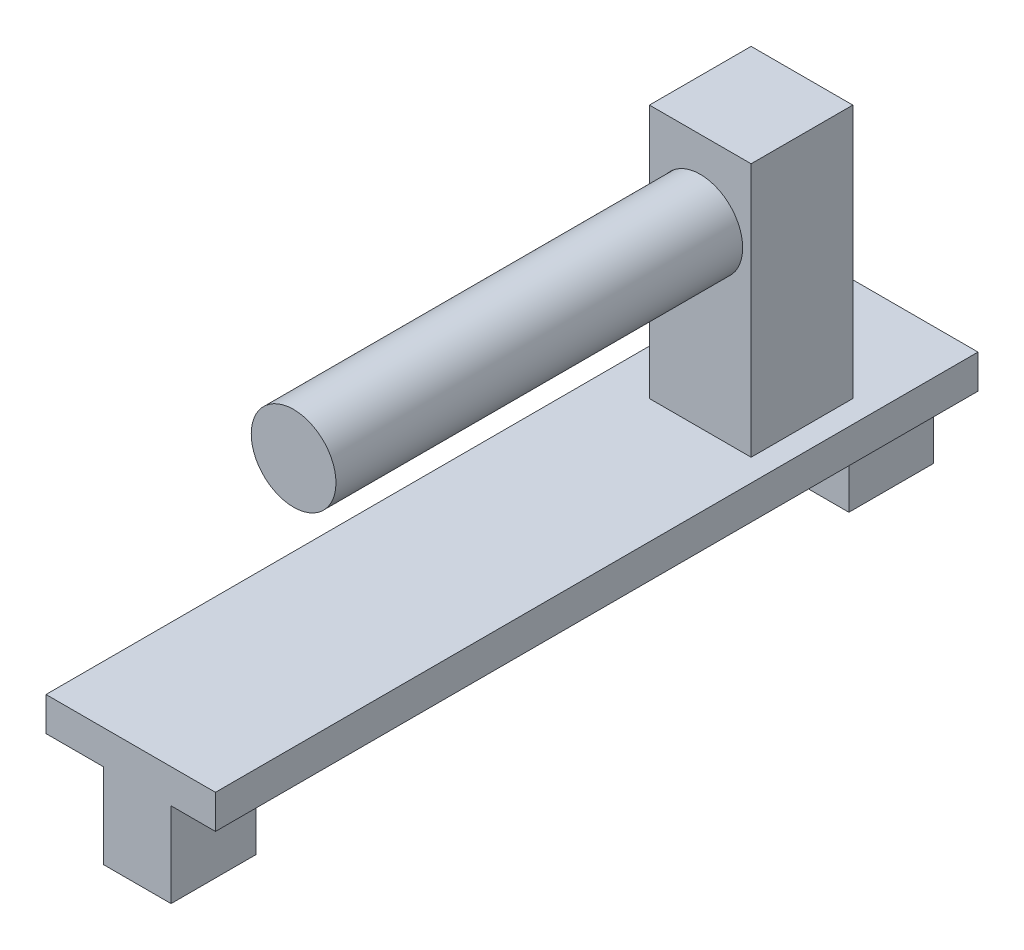
SolidWorks part; units mm, degrees
ref_plane "Front Plane" through (0, 0, 0) normal (0, 0, 1) x (1, 0, 0)
ref_plane "Top Plane" through (0, 0, 0) normal (0, 1, 0) x (1, 0, 0)
ref_plane "Right Plane" through (0, 0, 0) normal (1, 0, 0) x (0, 0, -1)
sketch "Sketch1" plane through (0, 0, 0) normal (0, 1, 0) x (1, 0, 0)
  line L1 (-3, -3) -> (3, -3)
  line L2 (-3, -3) -> (-3, 3)
  line L3 (-3, 3) -> (3, 3)
  line L4 (3, -3) -> (3, 3)
  line L5 (-3, -3) -> (3, 3) construction
  line L6 (-3, 3) -> (3, -3) construction
  point P0 (0, 0)
  dimension "D1" = 6
  dimension "D2" = 6
extrude "Boss-Extrude1" add sketch "Sketch1" along normal blind 15
sketch "Sketch3" plane through (0, 0, 0) normal (0, 1, 0) x (1, 0, 0)
  line L0 (4.3176, 9.0713) -> (-5.6824, 9.0713)
  line L1 (4.3176, 9.0713) -> (4.3176, -35.9287)
  line L2 (-5.6824, 9.0713) -> (-5.6824, -35.9287)
  line L3 (4.3176, -35.9287) -> (-5.6824, -35.9287)
  dimension "D1" = 45
  dimension "D2" = 10
extrude "Boss-Extrude2" add sketch "Sketch3" against normal blind 2
sketch "Sketch4" plane through (0, 0, 35.9287) normal (0, 0, 1) x (1, 0, 0)
  line L0 (-2.3022, -2) -> (1.6978, -2)
  line L1 (-2.3022, -2) -> (-2.3022, -7)
  line L2 (1.6978, -2) -> (1.6978, -7)
  line L3 (-2.3022, -7) -> (1.6978, -7)
  line L4 (-5.6824, -2) -> (4.3176, -2) construction
  dimension "D1" = 5
  dimension "D2" = 4
extrude "Boss-Extrude3" add sketch "Sketch4" against normal blind 2
sketch "Sketch5" plane through (0, 0, -9.0713) normal (0, 0, -1) x (-1, 0, 0)
  line L0 (-1.6978, -2) -> (2.3022, -2)
  line L1 (-1.6978, -2) -> (-1.6978, -7)
  line L2 (2.3022, -2) -> (2.3022, -7)
  line L3 (-1.6978, -7) -> (2.3022, -7)
  dimension "D1" = 4
  dimension "D2" = 5
extrude "Boss-Extrude4" add sketch "Sketch5" against normal blind 2
sketch "Sketch6" plane through (0, 0, 33.9287) normal (0, 0, -1) x (-1, 0, 0)
  line L0 (-1.6978, -7) -> (2.3022, -7)
  line L1 (-1.6978, -7) -> (-1.6978, -4)
  line L2 (2.3022, -7) -> (2.3022, -4)
  line L3 (-1.6978, -4) -> (2.3022, -4)
  line L4 (2.3022, -7) -> (-1.6978, -7) construction
  line L5 (2.3022, -2) -> (2.3022, -7) construction
  dimension "D1" = 3
extrude "Boss-Extrude5" add sketch "Sketch6" along normal blind 3
sketch "Sketch7" plane through (0, 0, -7.0713) normal (0, 0, 1) x (1, 0, 0)
  line L0 (1.6978, -7) -> (-2.3022, -7)
  line L1 (1.6978, -7) -> (1.6978, -4)
  line L2 (-2.3022, -7) -> (-2.3022, -4)
  line L3 (1.6978, -4) -> (-2.3022, -4)
  dimension "D1" = 3
extrude "Boss-Extrude6" add sketch "Sketch7" along normal blind 3
sketch "Sketch8" plane through (0, 0, 3) normal (0, 0, 1) x (1, 0, 0)
  circle A0 centre (0, 10.462) radius 2.5
  dimension "D1" = 5
extrude "Cut-Extrude1" cut sketch "Sketch8" against normal blind 1
sketch "Sketch9" plane through (0, 0, 2) normal (0, 0, 1) x (1, 0, 0)
  circle A0 centre (0, 10.4452) radius 2.5
  dimension "D1" = 5
extrude "Boss-Extrude7" add sketch "Sketch9" along normal blind 25
